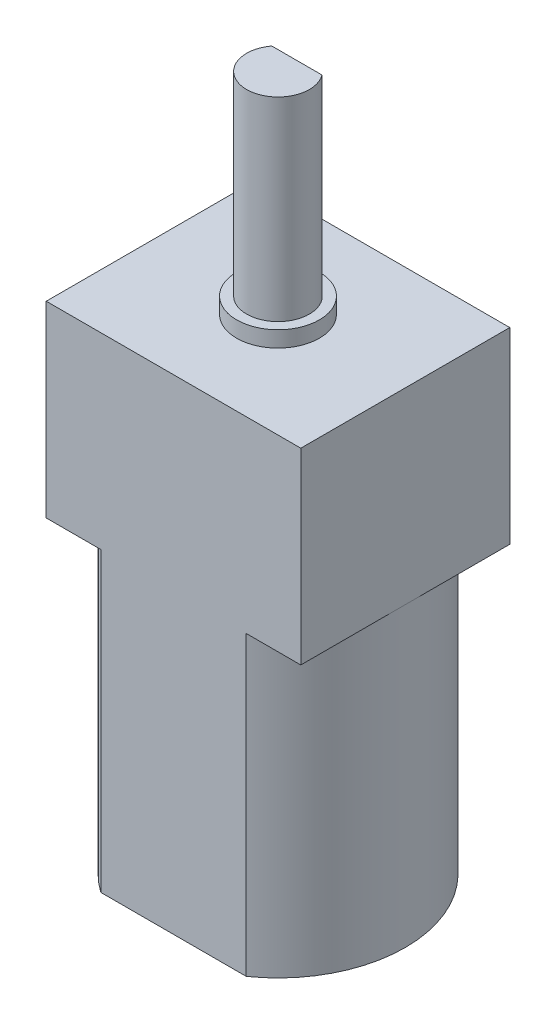
SolidWorks part; units mm, degrees
ref_plane "Front Plane" through (0, 0, 0) normal (0, 0, 1) x (1, 0, 0)
ref_plane "Top Plane" through (0, 0, 0) normal (0, 1, 0) x (1, 0, 0)
ref_plane "Right Plane" through (0, 0, 0) normal (1, 0, 0) x (0, 0, -1)
sketch "Sketch2" plane through (0, 0, 0) normal (0, 1, 0) x (1, 0, 0)
  line L1 (-3.427, 4.925) -> (3.427, 4.925)
  line L3 (-3.427, -4.925) -> (3.427, -4.925)
  arc A0 (-3.427, 4.925) -> (-3.427, -4.925) centre (0, 0) ccw
  arc A1 (3.427, -4.925) -> (3.427, 4.925) centre (0, 0) ccw
  dimension "D1" = 9.85
  dimension "D2" = 12
extrude "Boss-Extrude1" add sketch "Sketch2" along normal blind 14
sketch "Sketch3" plane through (0, 14, 0) normal (0, 1, 0) x (1, 0, 0)
  line L1 (6, 4.925) -> (-6, 4.925)
  line L2 (6, 4.925) -> (6, -4.925)
  line L3 (6, -4.925) -> (-6, -4.925)
  line L4 (-6, 4.925) -> (-6, -4.925)
extrude "Boss-Extrude2" add sketch "Sketch3" along normal blind 8.85
sketch "Sketch4" plane through (0, 22.85, 0) normal (0, 1, 0) x (1, 0, 0)
  circle A0 centre (0, 0) radius 1.95
extrude "Boss-Extrude3" add sketch "Sketch4" along normal blind 0.75
sketch "Sketch5" plane through (0, 23.6, 0) normal (0, 1, 0) x (1, 0, 0)
  line L0 (-1.1825, 0.89) -> (1.1825, 0.89)
  arc A0 (-1.1825, 0.89) -> (1.1825, 0.89) centre (0, 0) ccw
  point P5 (0, -1.48)
  dimension "D1" = 2.37
extrude "Boss-Extrude4" add sketch "Sketch5" along normal blind 9.17
sketch "Sketch6" plane through (0, 0, 0) normal (0, -1, 0) x (1, 0, 0)
  circle A0 centre (0, 0) radius 2.47
extrude "Boss-Extrude5" add sketch "Sketch6" along normal blind 1.14
